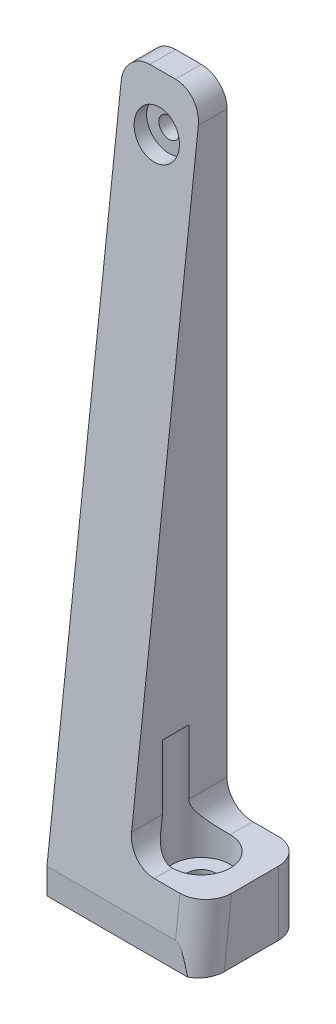
SolidWorks part; units mm, degrees
ref_plane "Plan de face" through (0, 0, 0) normal (0, 0, 1) x (1, 0, 0)
ref_plane "Plan de dessus" through (0, 0, 0) normal (0, 1, 0) x (1, 0, 0)
ref_plane "Plan de droite" through (0, 0, 0) normal (1, 0, 0) x (0, 0, -1)
sketch "Esquisse1" plane through (0, 0, 0) normal (0, 0, 1) x (1, 0, 0)
  line L0 (0, 0) -> (0, 8.7289) construction
  line L1 (0, 100) -> (-47.5, 100) construction
  line L2 (0, 100) -> (0, 0) construction
  line L3 (0, 0) -> (-37.5, 0) construction
  line L4 (-37.5, 0) -> (-37.5, 10.5665) construction
  line L5 (-53.5, 108) -> (-53.5, 0)
  line L6 (-47.5, 100) -> (-47.5, 0) construction
  line L7 (-47.5, 0) -> (-37.5, 0) construction
  line L8 (-53.5, 108) -> (-41.5, 108)
  line L9 (-41.5, 108) -> (-41.5, 0)
  line L10 (-41.5, 0) -> (-53.5, 0)
  circle A0 centre (-47.5, 100) radius 1.6
  point P11 (-45.2817, 0)
  dimension "D2" = 3.2
  dimension "D1" = 95
  dimension "D3" = 75
  dimension "D4" = 8
  dimension "D5" = 6
  dimension "D6" = 6
  dimension "D7" = 100
extrude "Boss.-Extru.1" add sketch "Esquisse1" along normal blind 4
sketch "Esquisse2" plane through (0, 0, 0) normal (0, -1, 0) x (1, 0, 0)
  line L0 (-41.5, 0) -> (-29.5, 0)
  line L1 (-29.5, 0) -> (-29.5, 16)
  line L2 (-29.5, 16) -> (-53.5, 16)
  line L3 (-53.5, 16) -> (-53.5, 4)
  line L4 (-53.5, 4) -> (-41.5, 4)
  line L5 (-41.5, 4) -> (-41.5, 0)
  line L6 (0, 0) -> (0, 37.892) construction
  circle A0 centre (-37.5, 8) radius 2.2
  dimension "D1" = 4.4
  dimension "D2" = 37.5
  dimension "D3" = 8
  dimension "D4" = 8
  dimension "D5" = 8
extrude "Boss.-Extru.2" add sketch "Esquisse2" against normal blind 4
sketch "Esquisse3" plane through (-53.5, 0, 0) normal (-1, 0, 0) x (0, 0, 1)
  line L0 (4, 108) -> (16, 4)
  line L1 (16, 4) -> (4, 4)
  line L2 (4, 4) -> (4, 108)
extrude "Boss.-Extru.3" add sketch "Esquisse3" against normal blind 12
sketch "Esquisse4" plane through (0, 4, 0) normal (0, 1, 0) x (1, 0, 0)
  line L4 (-41.5, 0) -> (-41.5, -16)
  line L5 (-41.5, -16) -> (-29.5, -16)
  line L6 (-29.5, -16) -> (-29.5, 0)
  line L7 (-29.5, 0) -> (-41.5, 0)
  line L8 (-41.5, 0) -> (-41.5, -16)
  line L9 (-41.5, -16) -> (-29.5, -16)
  line L10 (-29.5, -16) -> (-29.5, 0)
  line L11 (-29.5, 0) -> (-41.5, 0)
  circle A0 centre (-37.5, -8) radius 2.2 construction
  circle A1 centre (-37.5, -8) radius 2.2
  dimension "D1" = 0
extrude "Boss.-Extru.4" add sketch "Esquisse4" along normal blind 6
sketch "Esquisse5" plane through (-41.5, 0, 0) normal (-1, 0, 0) x (0, 0, 1)
  line L3 (15.3077, 10) -> (16, 4)
  line L4 (16, 4) -> (16, 10)
  line L5 (16, 10) -> (15.3077, 10)
  line L6 (15.3077, 10) -> (16, 4)
  line L7 (16, 4) -> (16, 10)
  line L8 (16, 10) -> (15.3077, 10)
  dimension "D1" = 0
extrude "Enlèv. mat.-Extru.1" cut sketch "Esquisse5" against normal through all
sketch "Esquisse6" plane through (0, 10, 0) normal (0, 1, 0) x (1, 0, 0)
  circle A0 centre (-37.5, -8) radius 4.5
  dimension "D1" = 9
extrude "Enlèv. mat.-Extru.2" cut sketch "Esquisse6" along normal blind 14
sketch "Esquisse8" plane through (0, 10, 0) normal (0, 1, 0) x (1, 0, 0)
  circle A0 centre (-37.5, -8) radius 4.5
extrude "Enlèv. mat.-Extru.3" cut sketch "Esquisse8" against normal blind 4
sketch "Esquisse9" plane through (0, 0, 0) normal (0, 0, -1) x (-1, 0, 0)
  circle A0 centre (47.5, 100) radius 1.6 construction
  circle A1 centre (47.5, 100) radius 1.6
extrude "Enlèv. mat.-Extru.4" cut sketch "Esquisse9" against normal through all
ref_plane "Plan1" through (0, 0, 3) normal (0, 0, -1) x (-1, 0, 0)
sketch "Esquisse10" plane through (0, 0, 3) normal (0, 0, -1) x (-1, 0, 0)
  circle A0 centre (47.5, 100) radius 3.5
  dimension "D1" = 7
extrude "Enlèv. mat.-Extru.5" cut sketch "Esquisse10" against normal through all
fillet "Congé1" radius 4 2 edges at (-41.5, 108, 2) (-53.5, 108, 2)
fillet "Congé2" radius 4 2 edges at (-41.5, 10, 12.6846) (-41.5, 10, 2.9692)
fillet "Congé3" radius 4 2 edges at (-29.5, 5, 0) (-29.5, 7, 15.6538)
